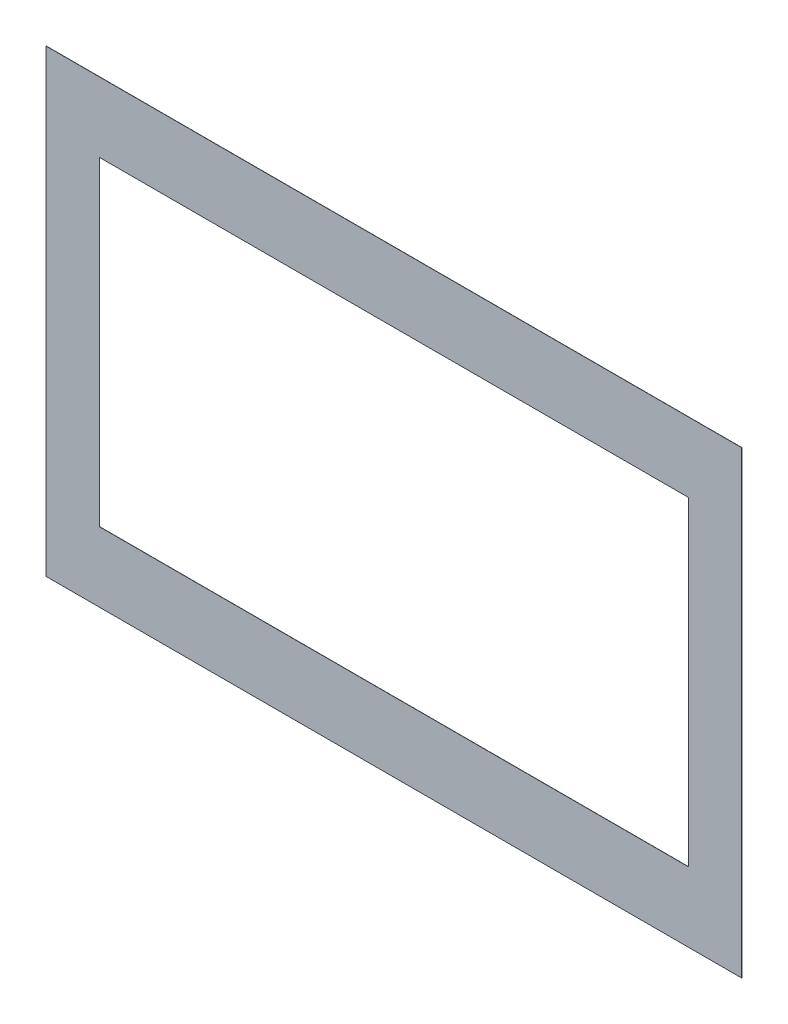
SolidWorks part; units mm, degrees
ref_plane "Front Plane" through (0, 0, 0) normal (0, 0, 1) x (1, 0, 0)
ref_plane "Top Plane" through (0, 0, 0) normal (0, 1, 0) x (1, 0, 0)
ref_plane "Right Plane" through (0, 0, 0) normal (1, 0, 0) x (0, 0, -1)
sketch "Sketch1" plane through (0, 0, 0) normal (0, 0, 1) x (1, 0, 0)
  line L1 (336.55, 222.25) -> (-336.55, 222.25)
  line L2 (336.55, 222.25) -> (336.55, -222.25)
  line L3 (336.55, -222.25) -> (-336.55, -222.25)
  line L4 (-336.55, 222.25) -> (-336.55, -222.25)
  line L5 (336.55, 222.25) -> (-336.55, -222.25) construction
  line L6 (336.55, -222.25) -> (-336.55, 222.25) construction
  point P0 (0, 0)
  dimension "D1" = 444.5
  dimension "D2" = 673.1
extrude "Boss-Extrude1" add sketch "Sketch1" along normal mid plane 0.2032
sketch "Sketch2" plane through (0, 0, 0.1016) normal (0, 0, 1) x (1, 0, 0)
  line L0 (0, 0) -> (0, -222.25) construction
  line L1 (284.9626, 154.7876) -> (-284.9626, 154.7876)
  line L2 (284.9626, 154.7876) -> (284.9626, -154.7876)
  line L3 (284.9626, -154.7876) -> (-284.9626, -154.7876)
  line L4 (-284.9626, 154.7876) -> (-284.9626, -154.7876)
  line L5 (284.9626, 154.7876) -> (-284.9626, -154.7876) construction
  line L6 (284.9626, -154.7876) -> (-284.9626, 154.7876) construction
  line L7 (-336.55, -222.25) -> (336.55, -222.25) construction
  point P0 (0, 0)
  dimension "D1" = 309.5752
  dimension "D2" = 569.9252
extrude "Cut-Extrude1" cut sketch "Sketch2" against normal through all both and the other way through all
sketch "Sketch4" plane through (0, 0, 0.1016) normal (0, 0, 1) x (1, 0, 0)
  line L0 (-336.55, 222.25) -> (-336.55, -222.25) construction
  line L1 (-336.55, 203.2) -> (-344.4875, 203.2)
  line L2 (-336.55, 203.2) -> (-336.55, -203.2)
  line L3 (-336.55, -203.2) -> (-344.4875, -203.2)
  line L4 (-344.4875, 203.2) -> (-344.4875, -203.2)
  line L5 (336.55, -222.25) -> (336.55, 222.25) construction
  line L6 (336.55, 203.2) -> (344.4875, 203.2)
  line L7 (336.55, 203.2) -> (336.55, -203.2)
  line L8 (336.55, -203.2) -> (344.4875, -203.2)
  line L9 (344.4875, 203.2) -> (344.4875, -203.2)
  line L10 (336.55, 222.25) -> (-336.55, 222.25) construction
  line L15 (0, 0) -> (0, 230.1875) construction
  line L16 (-336.55, -222.25) -> (336.55, -222.25) construction
  dimension "D1" = 19.05
  dimension "D2" = 19.05
  dimension "D3" = 7.9375
  dimension "D4" = 688.975
extrude "Boss-Extrude2" [suppressed] add sketch "Sketch4" against normal up to surface (15.875 mm away)
fillet "Fillet1" [suppressed] radius 6.35
sketch "Sketch6" plane through (336.55, 0, 0) normal (1, 0, 0) x (0, 0, -1)
  line L0 (-0.1016, -222.25) -> (0.1016, -222.1658)
  line L2 (0.1016, -222.1658) -> (0.1016, -222.25)
  line L3 (0.1016, -222.25) -> (-0.1016, -222.25)
  dimension "D1" = 22.5
extrude "Cut-Extrude4" [suppressed] cut sketch "Sketch6" against normal through all both and the other way through all
sketch "Sketch7" plane through (0, 0, -0.1016) normal (0, 0, -1) x (-1, 0, 0)
  line L11 (-304.0126, -173.8376) -> (304.0126, -173.8376)
  line L12 (304.0126, -173.8376) -> (304.0126, 173.8376)
  line L13 (304.0126, 173.8376) -> (-304.0126, 173.8376)
  line L14 (-304.0126, 173.8376) -> (-304.0126, -173.8376)
  line L15 (-297.6626, -173.8376) -> (297.6626, -173.8376)
  line L16 (304.0126, -167.4876) -> (304.0126, 167.4876)
  line L17 (297.6626, 173.8376) -> (-297.6626, 173.8376)
  line L18 (-304.0126, 167.4876) -> (-304.0126, -167.4876)
  arc A0 (304.0126, 167.4876) -> (297.6626, 173.8376) centre (297.6626, 167.4876) ccw
  arc A1 (297.6626, -173.8376) -> (304.0126, -167.4876) centre (297.6626, -167.4876) ccw
  arc A2 (-297.6626, -173.8376) -> (-304.0126, -167.4876) centre (-297.6626, -167.4876) cw
  arc A3 (-297.6626, 173.8376) -> (-304.0126, 167.4876) centre (-297.6626, 167.4876) ccw
  dimension "D2" = 6.35
  dimension "D1" = 19.05
extrude "Cut-Extrude5" [suppressed] cut sketch "Sketch7" against normal blind 12.7
